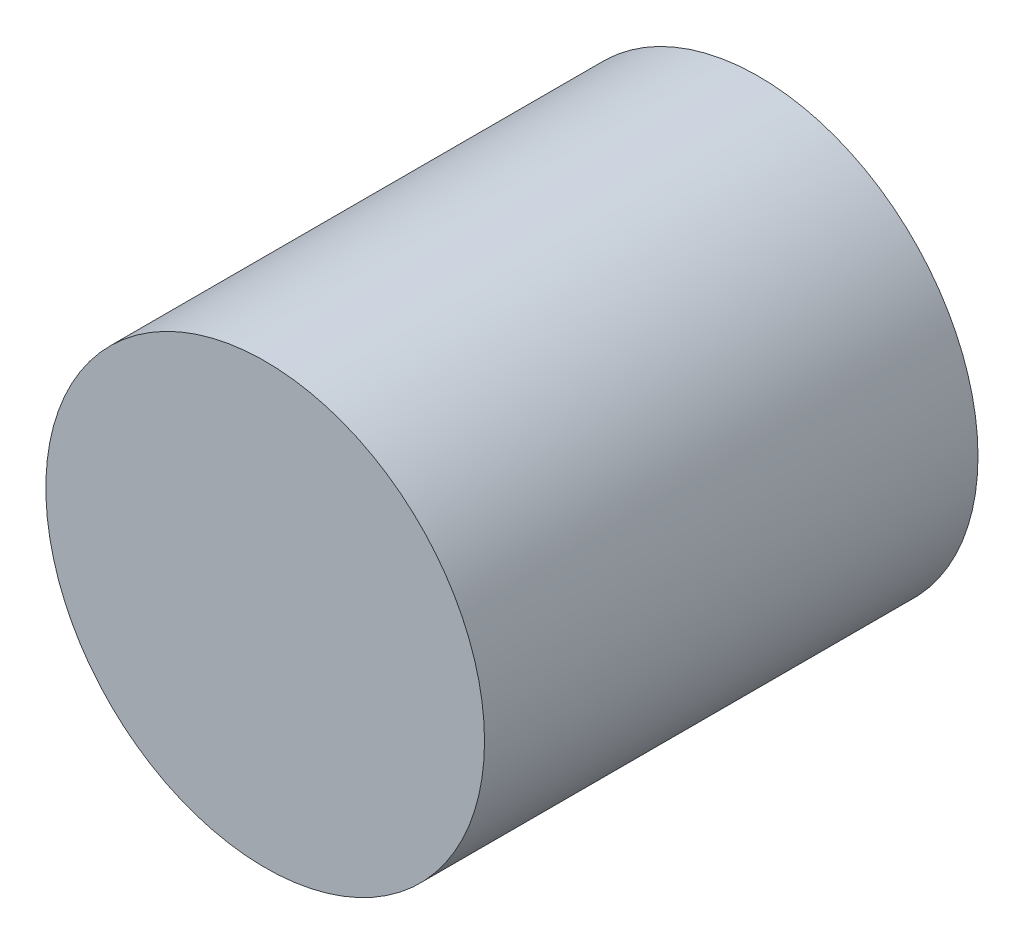
SolidWorks part; units mm, degrees
ref_plane "Front Plane" through (0, 0, 0) normal (0, 0, 1) x (1, 0, 0)
ref_plane "Top Plane" through (0, 0, 0) normal (0, 1, 0) x (1, 0, 0)
ref_plane "Right Plane" through (0, 0, 0) normal (1, 0, 0) x (0, 0, -1)
sketch "Sketch1" plane through (0, 0, 0) normal (0, 0, 1) x (1, 0, 0)
  circle A0 centre (6.35, 0) radius 1.778
  arc A1 (5.3246, -1.4525) -> (5.3246, 1.4525) centre (6.35, 0) ccw construction
extrude "Extrude1" add sketch "Sketch1" against normal blind 2.75 and the other way blind 1.25
